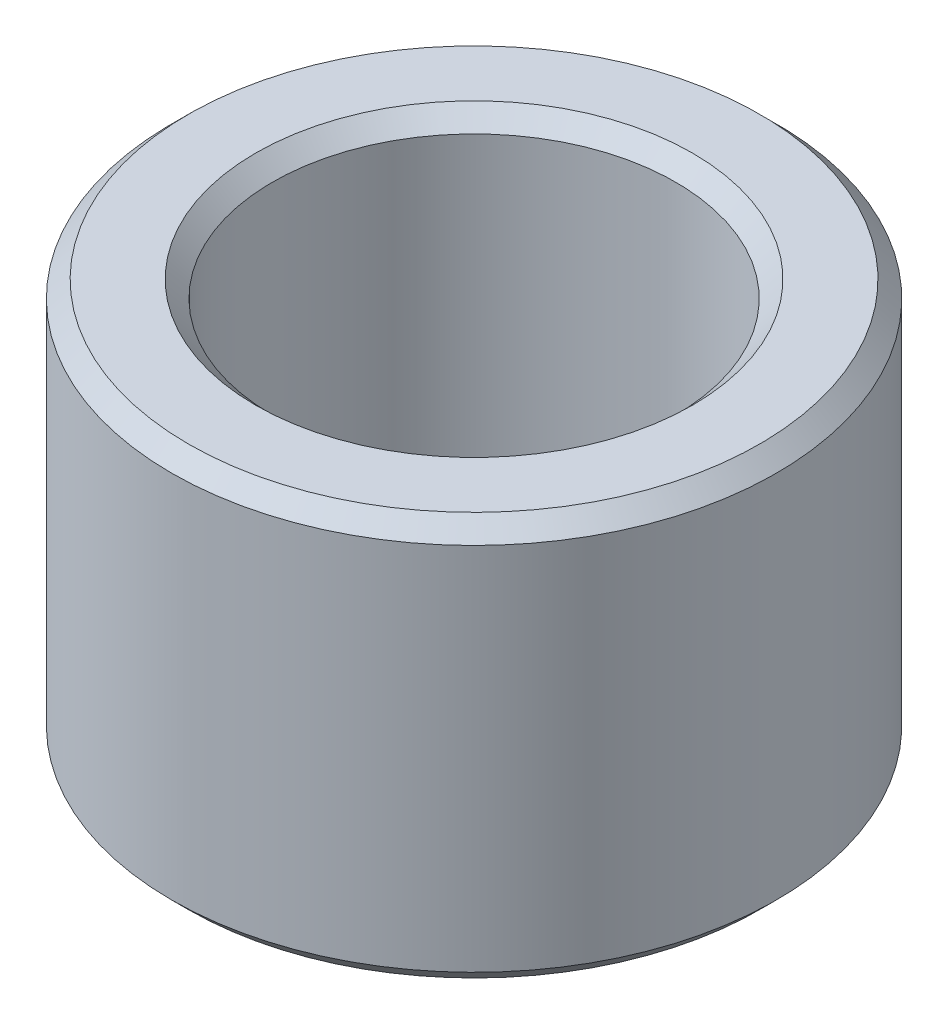
SolidWorks part; units mm, degrees
ref_plane "Plan de face" through (0, 0, 0) normal (0, 0, 1) x (1, 0, 0)
ref_plane "Plan de dessus" through (0, 0, 0) normal (0, 1, 0) x (1, 0, 0)
ref_plane "Plan de droite" through (0, 0, 0) normal (1, 0, 0) x (0, 0, -1)
sketch "Esquisse1" plane through (0, 0, 0) normal (0, 1, 0) x (1, 0, 0)
  circle A0 centre (0, 0) radius 9
  circle A1 centre (0, 0) radius 6
  dimension "D1" = 18
  dimension "D2" = 12
extrude "Boss.-Extru.1" add sketch "Esquisse1" along normal blind 12
chamfer "Chanfrein1" distance 0.5 angle 45 4 edges at (0, 0, 9) (0, 0, 6) (0, 12, 9) (0, 12, 6)
